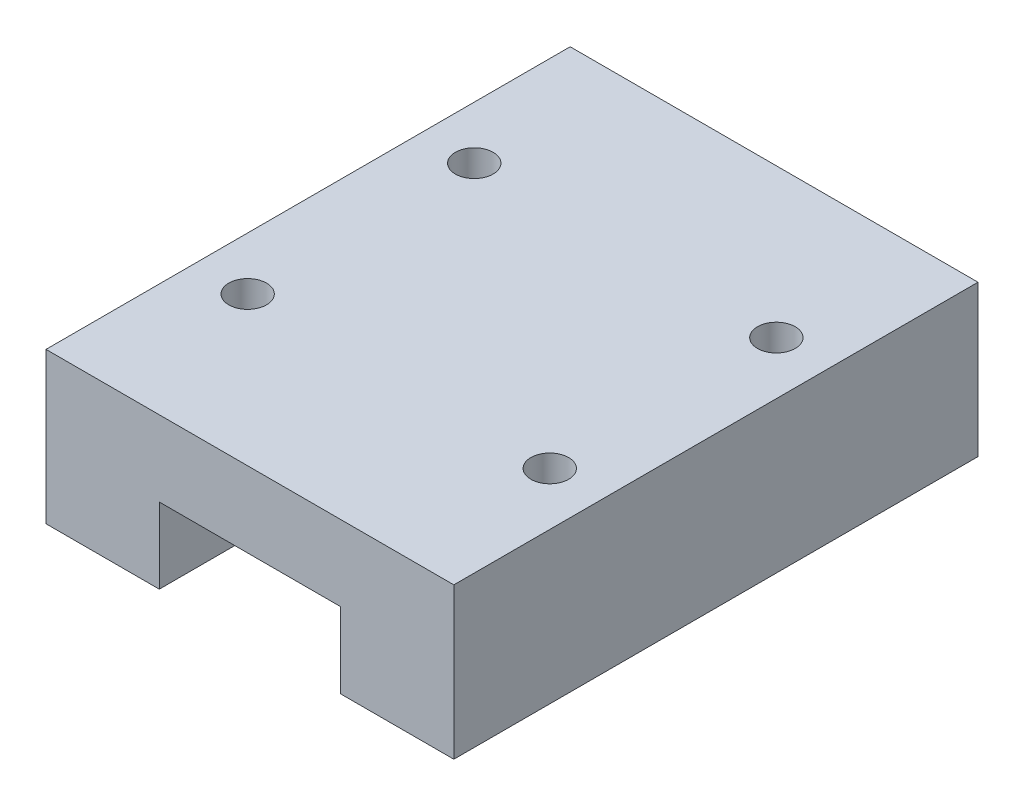
SolidWorks part; units mm, degrees
ref_plane "前视基准面" through (0, 0, 0) normal (0, 0, 1) x (1, 0, 0)
ref_plane "上视基准面" through (0, 0, 0) normal (0, 1, 0) x (1, 0, 0)
ref_plane "右视基准面" through (0, 0, 0) normal (1, 0, 0) x (0, 0, -1)
sketch "草图1" plane through (0, 0, 0) normal (0, 0, 1) x (1, 0, 0)
  line L1 (0, 0) -> (27, 0)
  line L2 (0, 0) -> (0, 10)
  line L3 (0, 10) -> (27, 10)
  line L4 (27, 0) -> (27, 10)
  dimension "D1" = 27
  dimension "D2" = 10
extrude "凸台-拉伸1" add sketch "草图1" along normal blind 34.7
sketch "草图2" plane through (0, 0, 0) normal (0, 0, -1) x (-1, 0, 0)
  line L0 (-13.5, 0) -> (-13.5, 32.626) construction
  line L1 (0, 0) -> (-27, 0) construction
  line L2 (-27, 10) -> (0, 10) construction
  line L3 (-19.5, 0) -> (-7.5, 0)
  line L4 (-19.5, 0) -> (-19.5, 5)
  line L5 (-19.5, 5) -> (-7.5, 5)
  line L6 (-7.5, 0) -> (-7.5, 5)
  dimension "D1" = 5
  dimension "D2" = 12
extrude "切除-拉伸1" cut sketch "草图2" against normal through all
hole_wizard "M3 螺纹孔1" positions "草图3" profile "草图4" tap size "M3" standard "ISO" end condition through all
sketch "草图3" plane through (0, 10, 0) normal (0, 1, 0) x (1, 0, 0)
  line L0 (13.5, -34.7) -> (13.5, 0) construction
  line L1 (27, -34.7) -> (0, -34.7) construction
  line L2 (27, 0) -> (0, 0) construction
  line L3 (13.5, 0) -> (13.5, -17.35) construction
  line L4 (13.5, -17.35) -> (-15.3114, -17.35) construction
  point P0 (23.5, -24.85)
  point P2 (23.5, -9.85)
  point P4 (3.5, -24.85)
  point P6 (3.5, -9.85)
  point P20 (0, 0)
  point P21 (0, 0)
  dimension "D1" = 15
  dimension "D2" = 20
sketch "草图4" plane through (23.5, 10, 24.85) normal (1, 0, 0) x (0, 0, 1)
  line L0 (0, 0) -> (0, 10)
  line L1 (0, 10) -> (1.25, 10)
  line L2 (1.25, 10) -> (1.25, 0)
  line L5 (1.25, 0) -> (0, 0)
  line L11 (0, -6.35) -> (0, 107.95) construction
  dimension "通孔螺纹孔钻头直径" = 2.5
  dimension "通孔螺纹孔钻头深度" = 10
cosmetic thread "孔螺蚊线1"
cosmetic thread "孔螺蚊线2"
cosmetic thread "孔螺蚊线3"
cosmetic thread "孔螺蚊线4"
